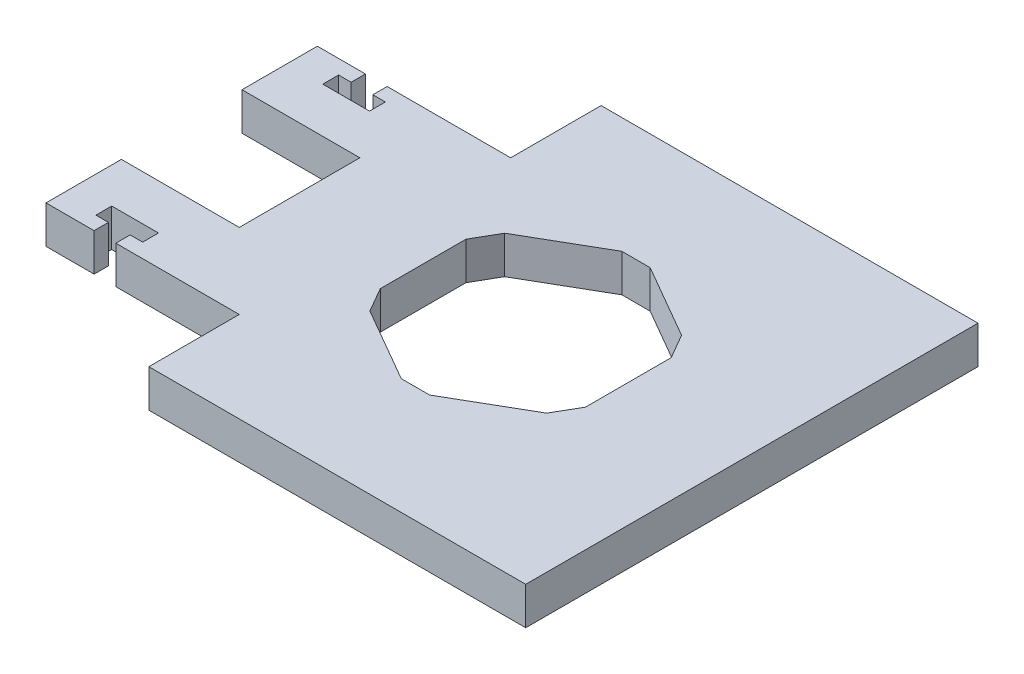
SolidWorks part; units mm, degrees
ref_plane "Front Plane" through (0, 0, 0) normal (0, 0, 1) x (1, 0, 0)
ref_plane "Top Plane" through (0, 0, 0) normal (0, 1, 0) x (1, 0, 0)
ref_plane "Right Plane" through (0, 0, 0) normal (1, 0, 0) x (0, 0, -1)
sketch "Sketch1" plane through (0, 0, 0) normal (0, 1, 0) x (1, 0, 0)
  line L0 (0, 0) -> (38.1, 0) construction
  line L1 (-25.4, -38.1) -> (38.1, -38.1)
  line L3 (-25.4, 38.1) -> (38.1, 38.1)
  line L4 (38.1, -38.1) -> (38.1, 38.1)
  line L5 (-38.1, -38.1) -> (38.1, 38.1) construction
  line L6 (-38.1, 38.1) -> (38.1, -38.1) construction
  line L7 (0, 0) -> (0, -18.5806) construction
  line L8 (-2.3893, -18.5806) -> (2.3893, -18.5806)
  line L9 (-17.2859, -7.2211) -> (-14.8966, -11.3595)
  line L10 (-14.8966, 11.3595) -> (-17.2859, 7.2211)
  line L11 (2.3893, 18.5806) -> (-2.3893, 18.5806)
  line L12 (17.2859, 7.2211) -> (14.8966, 11.3595)
  line L13 (14.8966, -11.3595) -> (17.2859, -7.2211)
  line L14 (2.3893, -18.5806) -> (14.8966, -11.3595)
  line L15 (-14.8966, -11.3595) -> (-2.3893, -18.5806)
  line L16 (-17.2859, 7.2211) -> (-17.2859, -7.2211)
  line L17 (-2.3893, 18.5806) -> (-14.8966, 11.3595)
  line L18 (14.8966, 11.3595) -> (2.3893, 18.5806)
  line L19 (17.2859, -7.2211) -> (17.2859, 7.2211)
  line L20 (-38.1, -22.86) -> (-46.2026, -22.86)
  line L21 (-57.9628, -22.86) -> (-57.9628, -10.16)
  line L22 (-57.9628, -10.16) -> (-38.1, -10.16)
  line L23 (-38.1, 22.86) -> (-46.2026, 22.86)
  line L24 (-57.9628, 22.86) -> (-57.9628, 10.16)
  line L25 (-57.9628, 10.16) -> (-38.1, 10.16)
  line L27 (-38.1, -10.16) -> (-38.1, 10.16)
  line L28 (-48.0314, -24.13) -> (-48.0314, -17.78) construction
  line L29 (-51.9684, -17.78) -> (-44.0944, -17.78)
  line L30 (-44.0944, -17.78) -> (-44.0944, -20.447)
  line L31 (-44.0944, -20.447) -> (-46.2026, -20.447)
  line L32 (-46.2026, -20.447) -> (-46.2026, -22.86)
  line L33 (-49.8602, -20.447) -> (-49.8602, -22.86)
  line L34 (-51.9684, -20.447) -> (-49.8602, -20.447)
  line L35 (-51.9684, -17.78) -> (-51.9684, -20.447)
  line L36 (-46.2026, 20.447) -> (-46.2026, 22.86)
  line L37 (-44.0944, 20.447) -> (-46.2026, 20.447)
  line L38 (-44.0944, 17.78) -> (-44.0944, 20.447)
  line L39 (-51.9684, 17.78) -> (-44.0944, 17.78)
  line L40 (-51.9684, 17.78) -> (-51.9684, 20.447)
  line L41 (-51.9684, 20.447) -> (-49.8602, 20.447)
  line L42 (-49.8602, 20.447) -> (-49.8602, 22.86)
  line L43 (-49.8602, -22.86) -> (-57.9628, -22.86)
  line L44 (-49.8602, 22.86) -> (-57.9628, 22.86)
  line L45 (-38.1, -22.86) -> (-25.4, -22.86)
  line L46 (-25.4, -22.86) -> (-25.4, -38.1)
  line L47 (-25.4, 22.86) -> (-25.4, 38.1)
  line L48 (-38.1, 22.86) -> (-25.4, 22.86)
  point P0 (0, 0)
  point P11 (0, -18.5806)
  point P25 (0, 0)
  point P35 (0, 0)
  dimension "D1" = 45
  dimension "D4" = 76.2
  dimension "D5" = 18.5806
  dimension "D6" = 17.2859
  dimension "D7" = 15.24
  dimension "D8" = 19.8628
  dimension "D9" = 20.32
  dimension "D10" = 7.874
  dimension "D11" = 5.08
  dimension "D12" = 2.667
  dimension "D13" = 3.6576
  dimension "D14" = 12.7
  dimension "D2" = 6
  dimension "D3" = 6
extrude "Boss-Extrude1" add sketch "Sketch1" against normal blind 6.35
